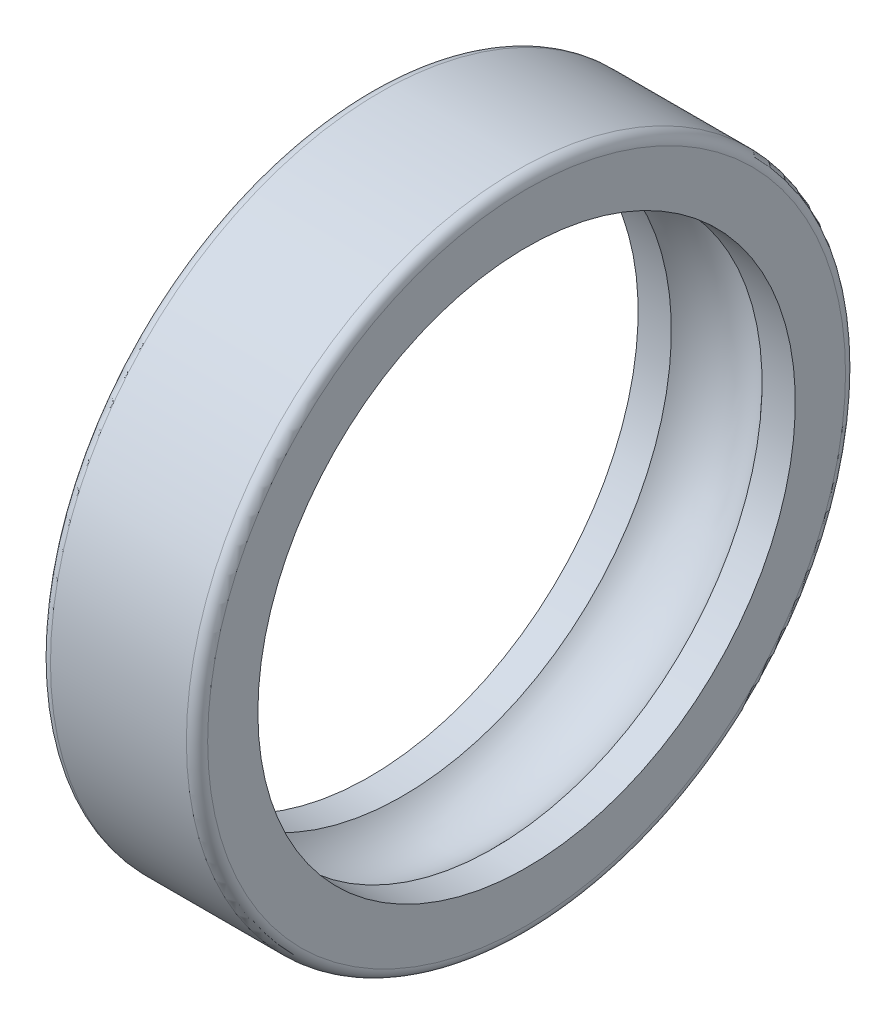
SolidWorks part; units mm, degrees
ref_plane "Front Plane" through (0, 0, 0) normal (0, 0, 1) x (1, 0, 0)
ref_plane "Top Plane" through (0, 0, 0) normal (0, 1, 0) x (1, 0, 0)
ref_plane "Right Plane" through (0, 0, 0) normal (1, 0, 0) x (0, 0, -1)
sketch "Sketch1" plane through (0, 0, 0) normal (0, 0, 1) x (1, 0, 0)
  line L0 (-33.1551, 0) -> (105.923, 0) construction
  line L2 (-15.5, 65) -> (15.5, 65)
  line L3 (-15.5, 65) -> (-15.5, 53)
  line L4 (-15.5, 53) -> (-8.9443, 53)
  line L5 (15.5, 65) -> (15.5, 53)
  line L6 (-15.5, 65) -> (15.5, 53) construction
  line L7 (-15.5, 53) -> (15.5, 65) construction
  line L8 (8.9443, 53) -> (15.5, 53)
  arc A0 (-8.9443, 53) -> (8.9443, 53) centre (0, 45) cw
  point P3 (0, 59)
  dimension "D5" = 12
  dimension "D1" = 53
  dimension "D2" = 65
  dimension "D3" = 31
  dimension "D4" = 8
revolve "Revolve1" add sketch "Sketch1" angle 360 about L0
fillet "Fillet1" radius 2.1 2 edges at (15.5, 0, 65) (-15.5, 0, 65)
